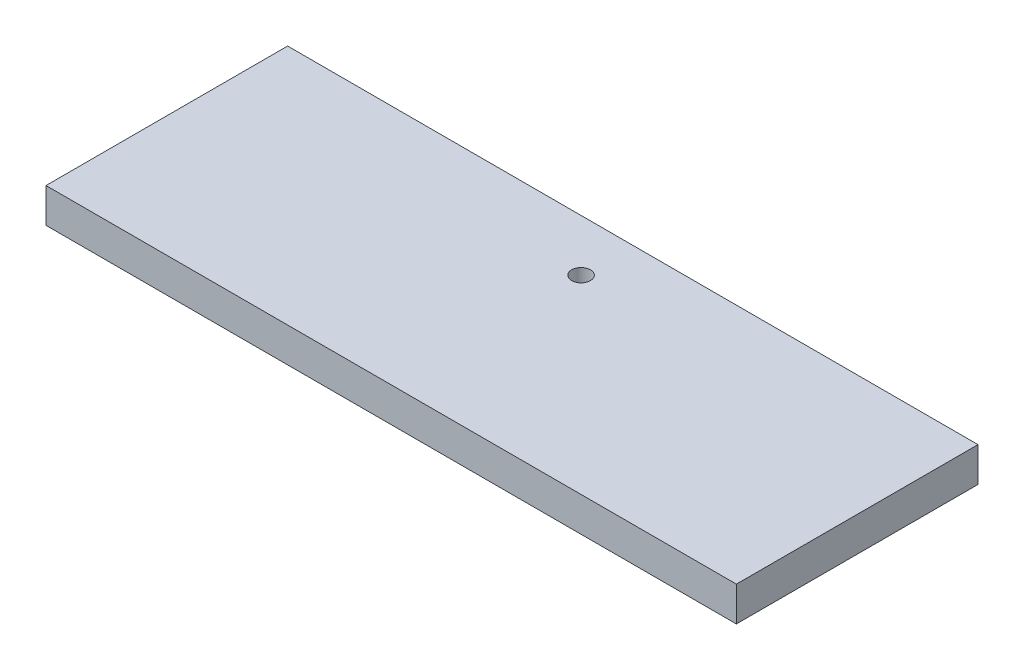
SolidWorks part; units mm, degrees
ref_plane "Front Plane" through (0, 0, 0) normal (0, 0, 1) x (1, 0, 0)
ref_plane "Top Plane" through (0, 0, 0) normal (0, 1, 0) x (1, 0, 0)
ref_plane "Right Plane" through (0, 0, 0) normal (1, 0, 0) x (0, 0, -1)
sketch "Sketch1" plane through (0, 0, 0) normal (0, 1, 0) x (1, 0, 0)
  line L0 (63.5, 0) -> (-63.5, 0) construction
  line L1 (-63.5, -22.225) -> (63.5, -22.225)
  line L2 (-63.5, -22.225) -> (-63.5, 22.225)
  line L3 (-63.5, 22.225) -> (63.5, 22.225)
  line L4 (63.5, -22.225) -> (63.5, 22.225)
  line L5 (-63.5, -22.225) -> (63.5, 22.225) construction
  line L6 (-63.5, 22.225) -> (63.5, -22.225) construction
  line L7 (60.325, -22.225) -> (60.325, 22.225) construction
  line L8 (-60.325, -22.225) -> (-60.325, 22.225) construction
  point P0 (0, 0)
  dimension "D1" = 44.45
  dimension "D2" = 127
  dimension "D3" = 3.175
  dimension "D4" = 3.175
extrude "Boss-Extrude1" add sketch "Sketch1" along normal blind 6.35
sketch "Sketch2" plane through (0, 6.35, 0) normal (0, 1, 0) x (1, 0, 0)
  line L0 (0, -22.225) -> (0, 22.225) construction
  line L1 (-63.5, -22.225) -> (63.5, -22.225) construction
  line L2 (63.5, 22.225) -> (-63.5, 22.225) construction
  circle A0 centre (0, 12.7) radius 1.7272
  dimension "D1" = 9.525
hole_wizard "#8-32 Tapped Hole1" positions "3DSketch1" profile "Sketch3" tap size "#8-32" standard "ANSI Inch"
sketch3d "3DSketch1"
  point P0 (0, 6.35, -12.7)
sketch "Sketch3" plane through (0, 6.35, -12.7) normal (1, 0, 0) x (0, 0, 1)
  line L0 (0, 0) -> (0, 13.4838)
  line L1 (0, 13.4838) -> (1.7272, 12.446)
  line L2 (1.7272, 12.446) -> (1.7272, 0)
  line L5 (1.7272, 0) -> (0, 0)
  line L10 (0, 13.4838) -> (-1.7272, 12.446) construction
  line L11 (0, -6.35) -> (0, 107.95) construction
  dimension "Tap Drill Dia." = 3.4544
  dimension "Tap Drill Depth" = 12.446
  dimension "Drill Angle" = 118
cosmetic thread "Hole Thread1" parameters "D1"=6.35, "D2"=4.1656
